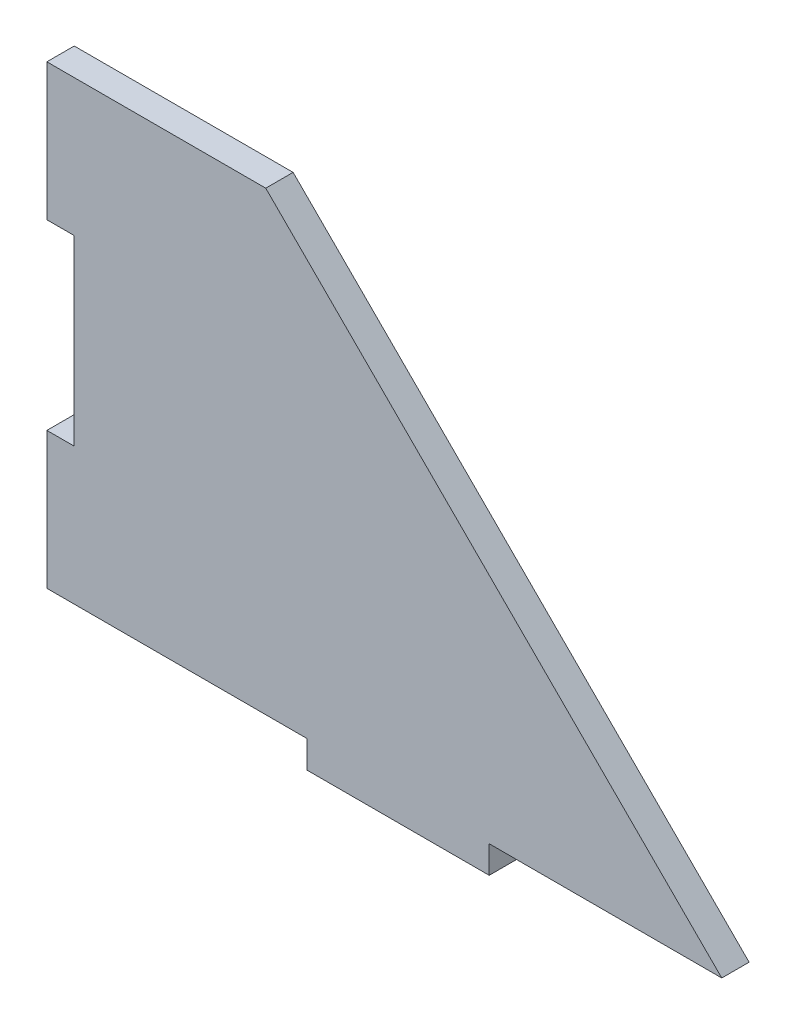
SolidWorks part; units mm, degrees
ref_plane "Alzado" through (0, 0, 0) normal (0, 0, 1) x (1, 0, 0)
ref_plane "Planta" through (0, 0, 0) normal (0, 1, 0) x (1, 0, 0)
ref_plane "Vista lateral" through (0, 0, 0) normal (1, 0, 0) x (0, 0, -1)
sketch "Croquis1" plane through (0, 0, 0) normal (0, 0, 1) x (1, 0, 0)
  line L0 (-14.5, 25) -> (35.5, -25)
  line L1 (-38.5, 25) -> (38.5, 25)
  line L2 (-38.5, 25) -> (-38.5, -25)
  line L3 (-38.5, -25) -> (38.5, -25)
  line L4 (38.5, 25) -> (38.5, -25)
  line L5 (-38.5, 25) -> (38.5, -25) construction
  line L6 (-38.5, -25) -> (38.5, 25) construction
  line L7 (-14.5, 25) -> (38.5, 25)
  point P0 (0, 0)
  dimension "D1" = 77
  dimension "D2" = 50
  dimension "D3" = 24
extrude "Saliente-Extruir1" add sketch "Croquis1" along normal blind 3
sketch "Croquis4" plane through (0, 0, 3) normal (0, 0, 1) x (1, 0, 0)
  line L0 (0, 0) -> (0, -17.2564) construction
  line L1 (-38.5, -25) -> (35.5, -25) construction
  line L2 (-10, -25) -> (10, -25)
  line L3 (-10, -25) -> (-10, -28)
  line L4 (-10, -28) -> (10, -28)
  line L5 (10, -25) -> (10, -28)
  dimension "D1" = 3
  dimension "D2" = 20
  dimension "D3" = 10
extrude "Saliente-Extruir3" add sketch "Croquis4" against normal blind 3
sketch "Croquis5" plane through (0, 0, 3) normal (0, 0, 1) x (1, 0, 0)
  line L0 (0, 0) -> (-54.0974, 0) construction
  line L1 (-38.5, 25) -> (-38.5, -25) construction
  line L2 (-38.5, 10) -> (-35.5, 10)
  line L3 (-38.5, 10) -> (-38.5, -10)
  line L4 (-38.5, -10) -> (-35.5, -10)
  line L5 (-35.5, 10) -> (-35.5, -10)
  dimension "D1" = 10
  dimension "D2" = 20
  dimension "D3" = 3
extrude "Cortar-Extruir1" cut sketch "Croquis5" against normal blind 3
